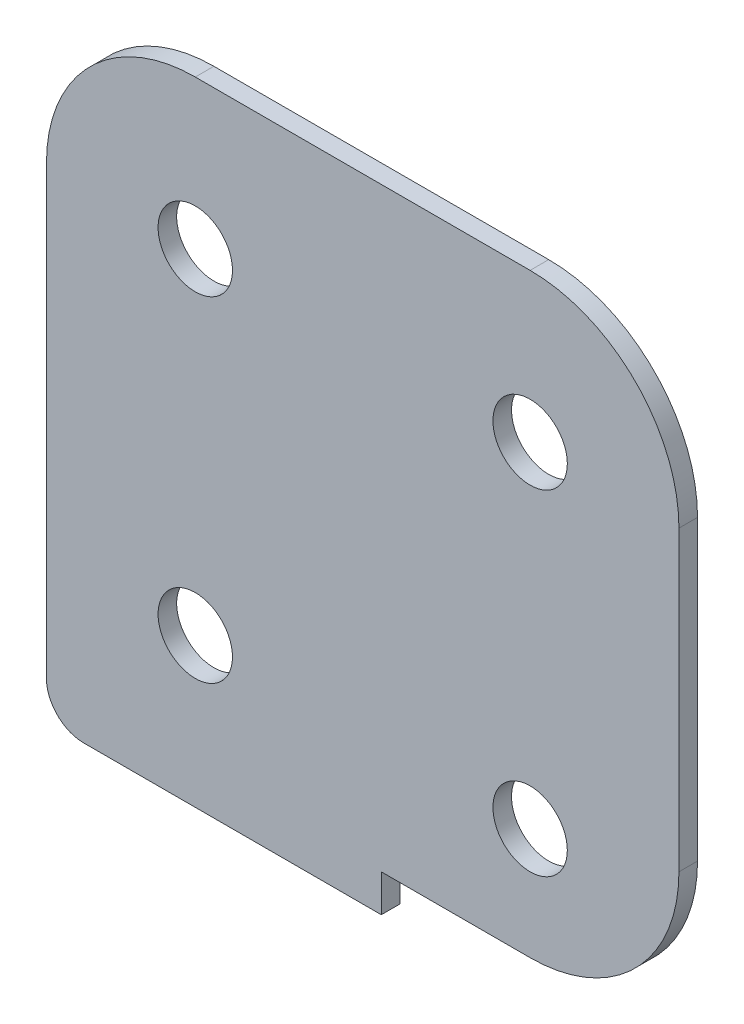
SolidWorks part; units mm, degrees
ref_plane "Front Plane" through (0, 0, 0) normal (0, 0, 1) x (1, 0, 0)
ref_plane "Top Plane" through (0, 0, 0) normal (0, 1, 0) x (1, 0, 0)
ref_plane "Right Plane" through (0, 0, 0) normal (1, 0, 0) x (0, 0, -1)
sketch "Sketch1" plane through (0, 0, 0) normal (0, 0, 1) x (1, 0, 0)
  line L0 (-12.7, 50.8) -> (-12.7, 0) construction
  line L2 (0, 0) -> (0, 50.8)
  line L3 (0, 50.8) -> (-53.975, 50.8)
  line L4 (-53.975, 0) -> (-53.975, 50.8)
  line L5 (-41.275, 50.8) -> (-41.275, -3.175) construction
  line L6 (-28.575, 38.1) -> (-25.4, 38.1) construction
  line L7 (-12.7, 25.4) -> (-12.7, 22.225) construction
  line L8 (-53.975, 0) -> (-53.975, -3.175)
  line L9 (-53.975, -3.175) -> (-25.4, -3.175)
  line L10 (0, -3.175) -> (0, 0) construction
  line L11 (-53.975, 0) -> (-25.4, 0) construction
  line L12 (-25.4, 0) -> (-25.4, -3.175)
  line L13 (-25.4, -3.175) -> (0, -3.175) construction
  line L15 (-25.4, 0) -> (-12.7, 0)
  circle A0 centre (-12.7, 38.1) radius 3.175
  circle A1 centre (-12.7, 9.525) radius 3.175
  circle A2 centre (-41.275, 9.525) radius 3.175
  circle A3 centre (-41.275, 38.1) radius 3.175
  circle A4 centre (-12.7, 38.1) radius 12.7 construction
  circle A5 centre (-12.7, 9.525) radius 12.7 construction
  circle A6 centre (-41.275, 38.1) radius 12.7 construction
  circle A7 centre (-41.275, 9.525) radius 12.7 construction
  arc A8 (-41.275, 50.8) -> (-53.975, 38.1) centre (-41.275, 38.1) ccw
  arc A9 (-12.7, 50.8) -> (0, 38.1) centre (-12.7, 38.1) cw
  arc A10 (-12.7, 0) -> (0, 12.7) centre (-12.7, 12.7) ccw
  point P17 (-12.7, 22.225)
  point P19 (-12.7, 25.4)
  point P23 (-28.575, 38.1)
  point P24 (-25.4, 38.1)
  point P34 (0, 0)
  dimension "D2" = 25.4
  dimension "D4" = 6.35
  dimension "D1" = 12.7
  dimension "D3" = 3.175
  dimension "D5" = 12.7
  dimension "D6" = 12.7
  dimension "D7" = 3.175
  dimension "D8" = 12.7
extrude "Boss-Extrude1" add sketch "Sketch1" along normal blind 1.5875
fillet "Fillet1" radius 3.175 1 edges at (-53.975, -3.175, 0.7937)
